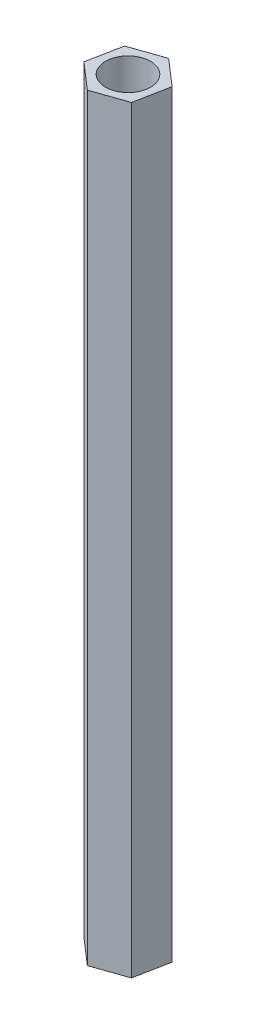
SolidWorks part; units mm, degrees
ref_plane "Front Plane" through (0, 0, 0) normal (0, 0, 1) x (1, 0, 0)
ref_plane "Top Plane" through (0, 0, 0) normal (0, 1, 0) x (1, 0, 0)
ref_plane "Right Plane" through (0, 0, 0) normal (1, 0, 0) x (0, 0, -1)
sketch "Sketch1" plane through (0, 0, 0) normal (0, 1, 0) x (1, 0, 0)
  line L1 (1.7449, -1.5128) -> (2.1826, 0.7547)
  line L2 (2.1826, 0.7547) -> (0.4377, 2.2676)
  line L3 (0.4377, 2.2676) -> (-1.7449, 1.5128)
  line L4 (-1.7449, 1.5128) -> (-2.1826, -0.7547)
  line L5 (-2.1826, -0.7547) -> (-0.4377, -2.2676)
  line L6 (-0.4377, -2.2676) -> (1.7449, -1.5128)
  circle A0 centre (0, 0) radius 2 construction
extrude "Boss-Extrude1" add sketch "Sketch1" along normal blind 50.5
sketch "Sketch2" plane through (0, 50.5, 0) normal (0, 1, 0) x (1, 0, 0)
  circle A0 centre (0, 0) radius 1.5
extrude "Cut-Extrude1" cut sketch "Sketch2" against normal through all
